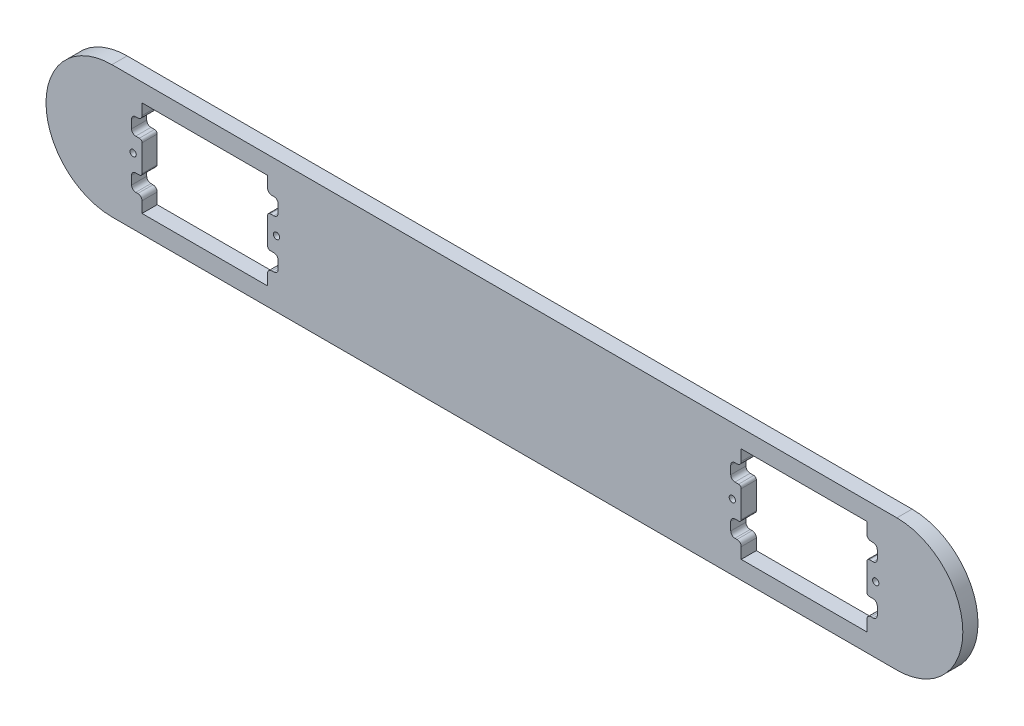
SolidWorks part; units mm, degrees
material "普通碳钢"
ref_plane "前视基准面" through (0, 0, 0) normal (0, 0, 1) x (1, 0, 0)
ref_plane "上视基准面" through (0, 0, 0) normal (0, 1, 0) x (1, 0, 0)
ref_plane "右视基准面" through (0, 0, 0) normal (1, 0, 0) x (0, 0, -1)
sketch "草图1" plane through (0, 0, 0) normal (0, 0, 1) x (1, 0, 0)
  line L0 (-75, 0) -> (75, 0) construction
  line L1 (-75, 12.6) -> (75, 12.6)
  line L2 (-75, -12.6) -> (75, -12.6)
  line L3 (0, 0) -> (0, 24.2406) construction
  line L4 (-57.25, 0) -> (-57.25, 14.1552) construction
  line L5 (-69.25, 6.25) -> (-45.25, 6.25)
  line L6 (-69.25, 6.25) -> (-69.25, -6.25)
  line L7 (-69.25, -6.25) -> (-45.25, -6.25)
  line L8 (-45.25, 6.25) -> (-45.25, -6.25)
  line L9 (-69.25, 6.25) -> (-45.25, -6.25) construction
  line L10 (-69.25, -6.25) -> (-45.25, 6.25) construction
  line L11 (69.25, 6.25) -> (69.25, -6.25)
  line L12 (69.25, 6.25) -> (45.25, 6.25)
  line L13 (45.25, 6.25) -> (45.25, -6.25)
  line L14 (69.25, -6.25) -> (45.25, -6.25)
  arc A0 (-75, 12.6) -> (-75, -12.6) centre (-75, 0) ccw
  arc A1 (75, -12.6) -> (75, 12.6) centre (75, 0) ccw
  circle A2 centre (-43.55, 0) radius 0.6
  circle A3 centre (-70.95, 0) radius 0.6
  circle A4 centre (-62.5, 0) radius 4 construction
  circle A5 centre (70.95, 0) radius 0.6
  circle A6 centre (62.5, 0) radius 4 construction
  circle A7 centre (43.55, 0) radius 0.6
  point P3 (0, 0)
  point P11 (-57.25, 0)
  dimension "D4" = 1.2
  dimension "D8" = 8
  dimension "D6" = 125
  dimension "D1" = 25.2
  dimension "D2" = 24
  dimension "D3" = 12.5
  dimension "D5" = 6.75
  dimension "D7" = 27.4
  dimension "D9" = 150
extrude "凸台-拉伸1" add sketch "草图1" along normal mid plane 2.9
sketch "草图2" plane through (0, 0, 1.45) normal (0, 0, 1) x (1, 0, 0)
  line L0 (44.45, 6.25) -> (44.05, 6.25)
  line L1 (45.25, 6.25) -> (45.25, -6.25) construction
  line L2 (43.25, 5.45) -> (43.25, 3.85)
  line L3 (44.05, 3.05) -> (45.25, 3.05)
  line L5 (69.25, 6.25) -> (45.25, 6.25) construction
  line L6 (45.25, 7.05) -> (45.25, 9.15)
  line L7 (45.25, 9.15) -> (69.25, 9.15)
  line L8 (69.25, 9.15) -> (69.25, 7.05)
  line L9 (57.25, 6.25) -> (57.25, 12.6) construction
  line L10 (75, 12.6) -> (-75, 12.6) construction
  line L11 (70.05, 6.25) -> (70.45, 6.25)
  line L12 (71.25, 5.45) -> (71.25, 3.85)
  line L13 (70.45, 3.05) -> (69.25, 3.05)
  line L14 (45.25, 3.05) -> (45.25, 6.25)
  line L15 (45.25, 6.25) -> (69.25, 6.25)
  line L16 (69.25, 6.25) -> (69.25, 3.05)
  line L17 (45.25, 0) -> (37.6082, 0) construction
  line L18 (44.05, -3.05) -> (45.25, -3.05)
  line L19 (43.25, -5.45) -> (43.25, -3.85)
  line L20 (44.45, -6.25) -> (44.05, -6.25)
  line L21 (45.25, -7.05) -> (45.25, -9.15)
  line L22 (45.25, -9.15) -> (69.25, -9.15)
  line L23 (69.25, -9.15) -> (69.25, -7.05)
  line L24 (70.05, -6.25) -> (70.45, -6.25)
  line L25 (71.25, -5.45) -> (71.25, -3.85)
  line L26 (70.45, -3.05) -> (69.25, -3.05)
  line L27 (69.25, -6.25) -> (69.25, -3.05)
  line L28 (45.25, -6.25) -> (69.25, -6.25)
  line L29 (45.25, -3.05) -> (45.25, -6.25)
  line L30 (0, 0) -> (0, 16.9532) construction
  line L31 (-45.25, 3.05) -> (-45.25, 6.25)
  line L32 (-44.05, 3.05) -> (-45.25, 3.05)
  line L33 (-43.25, 5.45) -> (-43.25, 3.85)
  line L34 (-44.45, 6.25) -> (-44.05, 6.25)
  line L35 (-45.25, 7.05) -> (-45.25, 9.15)
  line L36 (-45.25, 9.15) -> (-69.25, 9.15)
  line L37 (-69.25, 9.15) -> (-69.25, 7.05)
  line L38 (-70.05, 6.25) -> (-70.45, 6.25)
  line L39 (-71.25, 5.45) -> (-71.25, 3.85)
  line L40 (-70.45, 3.05) -> (-69.25, 3.05)
  line L41 (-69.25, 6.25) -> (-69.25, 3.05)
  line L42 (-45.25, 6.25) -> (-69.25, 6.25)
  line L43 (-45.25, -7.05) -> (-45.25, -9.15)
  line L44 (-44.45, -6.25) -> (-44.05, -6.25)
  line L45 (-43.25, -5.45) -> (-43.25, -3.85)
  line L46 (-44.05, -3.05) -> (-45.25, -3.05)
  line L47 (-45.25, -3.05) -> (-45.25, -6.25)
  line L48 (-45.25, -6.25) -> (-69.25, -6.25)
  line L49 (-69.25, -6.25) -> (-69.25, -3.05)
  line L50 (-70.45, -3.05) -> (-69.25, -3.05)
  line L51 (-71.25, -5.45) -> (-71.25, -3.85)
  line L52 (-70.05, -6.25) -> (-70.45, -6.25)
  line L53 (-69.25, -9.15) -> (-69.25, -7.05)
  line L54 (-45.25, -9.15) -> (-69.25, -9.15)
  arc A0 (70.45, 3.05) -> (71.25, 3.85) centre (70.45, 3.85) ccw
  arc A1 (70.45, 6.25) -> (71.25, 5.45) centre (70.45, 5.45) cw
  arc A2 (70.05, 6.25) -> (69.25, 7.05) centre (70.05, 7.05) cw
  arc A3 (45.25, 7.05) -> (44.45, 6.25) centre (44.45, 7.05) cw
  arc A4 (44.05, 6.25) -> (43.25, 5.45) centre (44.05, 5.45) ccw
  arc A5 (43.25, 3.85) -> (44.05, 3.05) centre (44.05, 3.85) ccw
  arc A6 (43.25, -3.85) -> (44.05, -3.05) centre (44.05, -3.85) cw
  arc A7 (44.05, -6.25) -> (43.25, -5.45) centre (44.05, -5.45) cw
  arc A8 (45.25, -7.05) -> (44.45, -6.25) centre (44.45, -7.05) ccw
  arc A9 (70.05, -6.25) -> (69.25, -7.05) centre (70.05, -7.05) ccw
  arc A10 (70.45, -6.25) -> (71.25, -5.45) centre (70.45, -5.45) ccw
  arc A11 (70.45, -3.05) -> (71.25, -3.85) centre (70.45, -3.85) cw
  arc A12 (-43.25, 3.85) -> (-44.05, 3.05) centre (-44.05, 3.85) cw
  arc A13 (-44.05, 6.25) -> (-43.25, 5.45) centre (-44.05, 5.45) cw
  arc A14 (-45.25, 7.05) -> (-44.45, 6.25) centre (-44.45, 7.05) ccw
  arc A15 (-70.05, 6.25) -> (-69.25, 7.05) centre (-70.05, 7.05) ccw
  arc A16 (-70.45, 6.25) -> (-71.25, 5.45) centre (-70.45, 5.45) ccw
  arc A17 (-70.45, 3.05) -> (-71.25, 3.85) centre (-70.45, 3.85) cw
  arc A18 (-45.25, -7.05) -> (-44.45, -6.25) centre (-44.45, -7.05) cw
  arc A19 (-44.05, -6.25) -> (-43.25, -5.45) centre (-44.05, -5.45) ccw
  arc A20 (-43.25, -3.85) -> (-44.05, -3.05) centre (-44.05, -3.85) ccw
  arc A21 (-70.45, -3.05) -> (-71.25, -3.85) centre (-70.45, -3.85) ccw
  arc A22 (-70.45, -6.25) -> (-71.25, -5.45) centre (-70.45, -5.45) cw
  arc A23 (-70.05, -6.25) -> (-69.25, -7.05) centre (-70.05, -7.05) cw
  point P21 (71.25, 3.05)
  point P24 (71.25, 6.25)
  point P27 (69.25, 6.25)
  point P30 (45.25, 6.25)
  point P33 (43.25, 6.25)
  point P36 (43.25, 3.05)
  dimension "D4" = 0.8
  dimension "D1" = 3.2
  dimension "D2" = 2
  dimension "D3" = 2.9
extrude "切除-拉伸1" cut sketch "草图2" against normal blind 3
fillet "圆角1" radius 0.5 8 edges at (-69.25, -3.05, 0) (-69.25, 3.05, 0) (-45.25, -3.05, 0) (-45.25, 3.05, 0) (69.25, -3.05, 0) (69.25, 3.05, 0) (45.25, -3.05, 0) (45.25, 3.05, 0)
